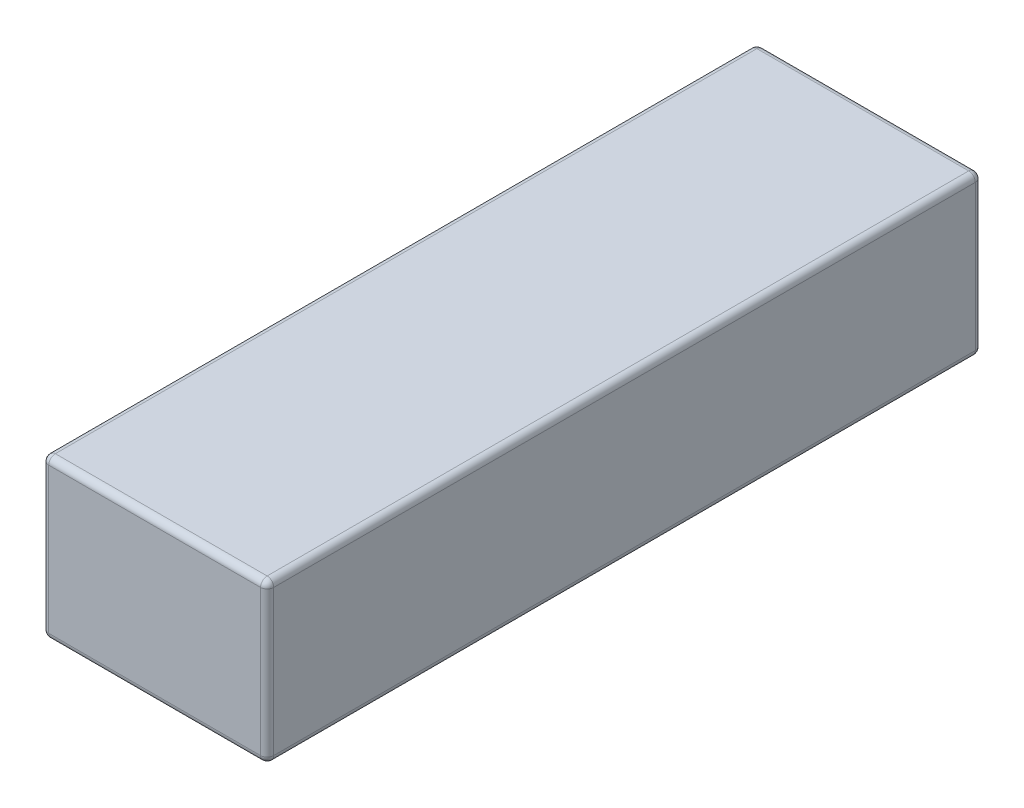
SolidWorks part; units mm, degrees
material "Brass"
ref_plane "Front Plane" through (0, 0, 0) normal (0, 0, 1) x (1, 0, 0)
ref_plane "Top Plane" through (0, 0, 0) normal (0, 1, 0) x (1, 0, 0)
ref_plane "Right Plane" through (0, 0, 0) normal (1, 0, 0) x (0, 0, -1)
sketch "Sketch1" plane through (0, 0, 0) normal (0, 0, 1) x (1, 0, 0)
  line L0 (-17, 12) -> (17, -12) construction
  line L1 (-17, 12) -> (17, 12)
  line L2 (-17, 12) -> (-17, -12)
  line L3 (-17, -12) -> (17, -12)
  line L4 (17, 12) -> (17, -12)
  dimension "D1" = 34
  dimension "D2" = 24
extrude "Boss-Extrude1" add sketch "Sketch1" along normal blind 108
fillet "Fillet1" radius 1 12 edges at (0, 12, 0) (0, 12, 108) (-17, 12, 54) (-17, 0, 108) (-17, 0, 0) (-17, -12, 54) (0, -12, 108) (0, -12, 0) (17, -12, 54) (17, 0, 108) (17, 12, 54) (17, 0, 0)
